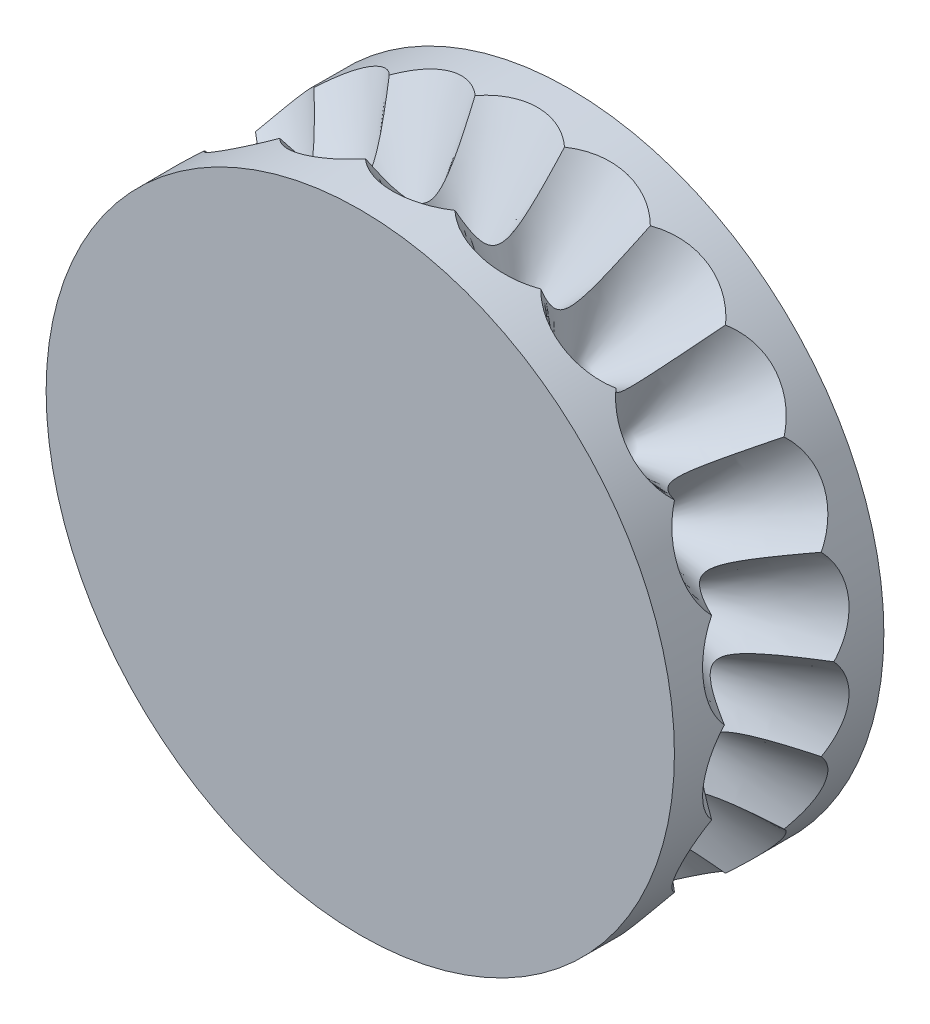
SolidWorks part; units mm, degrees
ref_plane "Front Plane" through (0, 0, 0) normal (0, 0, 1) x (1, 0, 0)
ref_plane "Top Plane" through (0, 0, 0) normal (0, 1, 0) x (1, 0, 0)
ref_plane "Right Plane" through (0, 0, 0) normal (1, 0, 0) x (0, 0, -1)
sketch "Sketch1" plane through (0, 0, 0) normal (0, 0, 1) x (1, 0, 0)
  circle A0 centre (0, 0) radius 6
  dimension "D1" = 12
extrude "Boss-Extrude1" add sketch "Sketch1" along normal mid plane 4
sketch "Sketch2" plane through (0, 0, 0) normal (0, 0, 1) x (1, 0, 0)
  line L0 (0, 0) -> (0, 7.6555) construction
  line L1 (0, 3.6) -> (2.3414, 7.6555)
  line L2 (2.3414, 7.6555) -> (0, 7.6555)
  line L3 (0, 7.6555) -> (0, 3.6)
  dimension "D1" = 3.6
  dimension "D2" = 30
revolve "Cut-Revolve1" cut sketch "Sketch2" angle 360 about L0
pattern_circular "CirPattern1" count 22 over 360 about axis through (0, 0, 2) along (0, 0, -1) of "Cut-Revolve1"
sketch "Sketch5" plane through (0, 0, 0) normal (1, 0, 0) x (0, 0, -1)
  circle A0 centre (0, 5.8) radius 0.875
  dimension "D1" = 1.75
  dimension "D2" = 5.8
extrude "Boss-Extrude2" [suppressed] add sketch "Sketch5" along normal mid plane 10 contours A0
